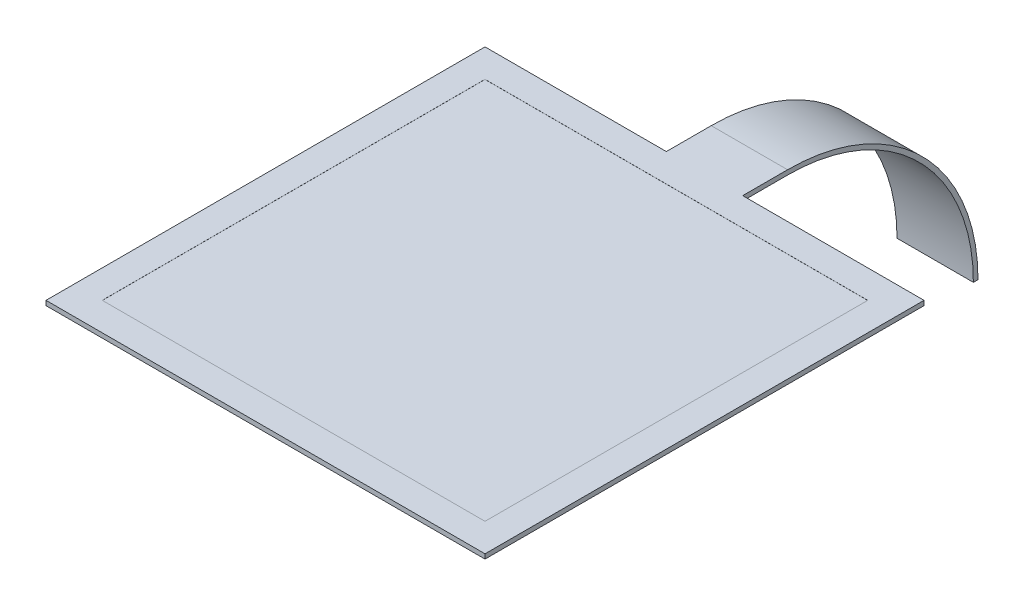
SolidWorks part; units mm, degrees
ref_plane "Front Plane" through (0, 0, 0) normal (0, 0, 1) x (1, 0, 0)
ref_plane "Top Plane" through (0, 0, 0) normal (0, 1, 0) x (1, 0, 0)
ref_plane "Right Plane" through (0, 0, 0) normal (1, 0, 0) x (0, 0, -1)
sketch "Sketch1" plane through (0, 0, 0) normal (0, 1, 0) x (1, 0, 0)
  line L0 (3.8, 21.85) -> (21.85, 21.85)
  line L1 (-21.85, 21.85) -> (-3.8, 21.85)
  line L2 (-21.85, 21.85) -> (-21.85, -21.85)
  line L3 (-21.85, -21.85) -> (21.85, -21.85)
  line L4 (21.85, 21.85) -> (21.85, -21.85)
  line L5 (-21.85, 21.85) -> (21.85, -21.85) construction
  line L6 (-21.85, -21.85) -> (21.85, 21.85) construction
  line L8 (-3.8, 21.85) -> (-3.8, 61.95)
  line L9 (-3.8, 61.95) -> (3.8, 61.95)
  line L10 (3.8, 21.85) -> (3.8, 61.95)
  point P0 (0, 0)
  point P10 (0, 61.95)
  dimension "D1" = 43.7
  dimension "D2" = 43.7
  dimension "D3" = 7.6
  dimension "D4" = 83.8
extrude "Boss-Extrude1" add sketch "Sketch1" along normal mid plane 0.46
sketch "Sketch2" plane through (0, 0.23, 0) normal (0, 1, 0) x (1, 0, 0)
  line L1 (-19.05, -19.05) -> (19.05, -19.05)
  line L2 (-19.05, -19.05) -> (-19.05, 19.05)
  line L3 (-19.05, 19.05) -> (19.05, 19.05)
  line L4 (19.05, -19.05) -> (19.05, 19.05)
  line L5 (-19.05, -19.05) -> (19.05, 19.05) construction
  line L6 (-19.05, 19.05) -> (19.05, -19.05) construction
  point P0 (0, 0)
  dimension "D1" = 38.1
extrude "Cut-Extrude1" cut sketch "Sketch2" against normal blind 0.01
sketch "Sketch3" plane through (0, 0, 0) normal (1, 0, 0) x (0, 0, -1)
  line L0 (21.85, -0.23) -> (61.95, -0.23) construction
  line L1 (26.3156, 0.23) -> (26.3156, -0.23)
  line L2 (44.8119, -18.7263) -> (45.2719, -18.7263)
  arc A0 (26.3156, -0.23) -> (44.8119, -18.7263) centre (26.3156, -18.7263) cw
  arc A1 (26.3156, 0.23) -> (45.2719, -18.7263) centre (26.3156, -18.7263) cw
  dimension "D1" = 0.46
extrude "Boss-Extrude2" add sketch "Sketch3" along normal mid plane 7.6
sketch "Sketch4" plane through (0, 0, 0) normal (1, 0, 0) x (0, 0, -1)
  line L0 (30.4663, -0.23) -> (61.95, -0.23) construction
  line L1 (21.85, 0.23) -> (61.95, 0.23) construction
  line L2 (61.95, 0.23) -> (61.95, -0.23) construction
  line L3 (30.4663, -0.23) -> (61.95, -0.23)
  line L4 (26.3156, 0.23) -> (61.95, 0.23)
  line L5 (61.95, 0.23) -> (61.95, -0.23)
  arc A0 (45.2719, -18.7263) -> (30.4663, -0.23) centre (26.3156, -18.7263) ccw construction
  arc A1 (30.4663, -0.23) -> (26.3156, 0.23) centre (26.3156, -18.7263) ccw
extrude "Cut-Extrude2" cut sketch "Sketch4" against normal mid plane 7.6
